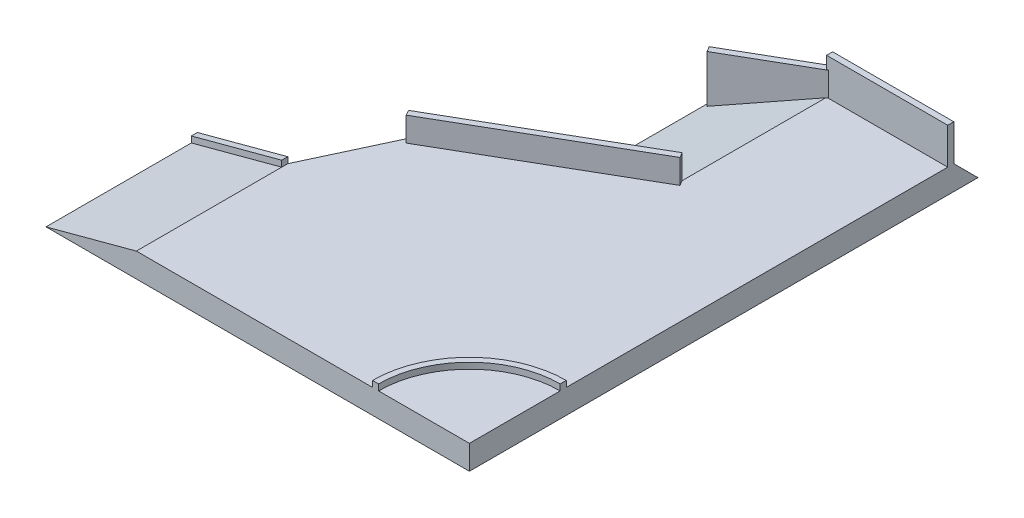
SolidWorks part; units mm, degrees
ref_plane "前视基准面" through (0, 0, 0) normal (0, 0, 1) x (1, 0, 0)
ref_plane "上视基准面" through (0, 0, 0) normal (0, 1, 0) x (1, 0, 0)
ref_plane "右视基准面" through (0, 0, 0) normal (1, 0, 0) x (0, 0, -1)
sketch "草图1" plane through (0, 0, 0) normal (0, 1, 0) x (1, 0, 0)
  line L0 (-2750, -1500) -> (-2116.0726, -140.5383)
  line L1 (-2750, -4000) -> (2750, -4000)
  line L2 (-2750, -4000) -> (-2750, -1500)
  line L3 (750, 4000) -> (2750, 4000)
  line L4 (2750, -4000) -> (2750, 4000)
  line L5 (-2750, -4000) -> (2750, 4000) construction
  line L6 (-532.1025, 773.9673) -> (2750, -4000) construction
  line L7 (-2116.0726, -140.5383) -> (750, 1514.1895)
  line L8 (750, 1514.1895) -> (750, 4000)
  point P0 (0, 0)
  dimension "D1" = 8000
  dimension "D2" = 5500
  dimension "D3" = 2500
  dimension "D4" = 2000
  dimension "D5" = 1500
  dimension "D6" = 120
  dimension "D7" = 145
  dimension "D8" = 90
extrude "凸台-拉伸1" add sketch "草图1" along normal blind 400
sketch "草图2" plane through (0, 400, 0) normal (0, 1, 0) x (1, 0, 0)
  line L0 (1150, -4000) -> (1250, -4000)
  line L1 (2750, -2500) -> (2750, -2400)
  arc A0 (2750, -2500) -> (1250, -4000) centre (2750, -4000) ccw
  arc A1 (2750, -2400) -> (1150, -4000) centre (2750, -4000) ccw
  dimension "D1" = 3200
  dimension "D2" = 3000
extrude "凸台-拉伸2" add sketch "草图2" along normal blind 100
sketch "草图3" plane through (0, 400, 0) normal (0, 1, 0) x (1, 0, 0)
  line L0 (750, 4000) -> (750, 1514.1895) construction
  line L1 (2750, 4000) -> (750, 4000)
  line L2 (2750, 4000) -> (2750, 3900)
  line L3 (2750, 3900) -> (750, 3900)
  line L4 (750, 4000) -> (750, 3900)
  dimension "D1" = 100
extrude "凸台-拉伸3" add sketch "草图3" along normal blind 600
sketch "草图4" plane through (0, 400, 0) normal (0, 1, 0) x (1, 0, 0)
  line L0 (750, 1514.1895) -> (-2116.0726, -140.5383)
  line L1 (750, 1514.1895) -> (800, 1427.5869)
  line L2 (-2116.0726, -140.5383) -> (-2066.0726, -227.1409)
  line L3 (800, 1427.5869) -> (-2066.0726, -227.1409)
  dimension "D1" = 100
extrude "凸台-拉伸4" add sketch "草图4" along normal blind 400
sketch "草图5" plane through (0, 0, 4000) normal (0, 0, 1) x (1, 0, 0)
  line L0 (-2750, 400) -> (-2750, 0)
  line L1 (-2750, 0) -> (-4242.8203, 0)
  line L2 (-4242.8203, 0) -> (-2750, 400)
  dimension "D1" = 15
extrude "凸台-拉伸5" add sketch "草图5" against normal blind 2500
sketch "草图6" plane through (0, 0, 1500) normal (0, 0, -1) x (-1, 0, 0)
  line L0 (2750, 400) -> (4242.8203, 0)
  line L1 (4242.8203, 0) -> (4242.8203, 100)
  line L2 (4242.8203, 100) -> (2750, 500)
  line L3 (2750, 500) -> (2750, 400)
  dimension "D1" = 100
extrude "凸台-拉伸6" add sketch "草图6" against normal blind 100
sketch "草图7" plane through (-1647.9093, 0, 951.4209) normal (-0.866, 0, 0.5) x (0.5, 0, 0.866)
  line L0 (-936.3265, 0) -> (-1336.3265, 0)
  line L1 (-1336.3265, 0) -> (-936.3265, 400)
  line L2 (-936.3265, 400) -> (-936.3265, 0)
  dimension "D1" = 45
extrude "凸台-拉伸7" add sketch "草图7" against normal up to next
ref_plane "基准面1" through (-1544.5508, 0, -2675.2405) normal (0.5, 0, 0.866) x (0, -1, 0)
sketch "草图8" plane through (-1544.5508, 0, -2675.2405) normal (0.5, 0, 0.866) x (0, -1, 0)
  line L0 (0, 2649.5191) -> (-400, 2649.5191)
  line L1 (-1000, 2649.5191) -> (0, 2649.5191) construction
  line L2 (-400, 2649.5191) -> (0, 1156.6987)
  line L3 (0, 1156.6987) -> (0, 2649.5191)
  dimension "D1" = 400
  dimension "D2" = 15
extrude "凸台-拉伸8" add sketch "草图8" along direction (0, 0, 1) on the side of the normal up to surface (2485.8105 mm away)
sketch "草图9" plane through (2750, 0, 0) normal (1, 0, 0) x (0, 0, -1)
  line L0 (4000, 0) -> (4400, 0)
  line L1 (4400, 0) -> (4000, 400)
  line L2 (4000, 1000) -> (4000, 0) construction
  line L3 (4000, 400) -> (4000, 0)
  dimension "D1" = 400
  dimension "D2" = 45
ref_plane "基准面3" through (2294.5508, 0, -1324.7595) normal (-0.866, 0, 0.5) x (0, 1, 0)
ref_plane "基准面4" through (1699.7595, 0, -455.4492) normal (-0.9659, 0, 0.2588) x (0, 1, 0)
extrude "凸台-拉伸10" add sketch "草图9" against normal up to surface (2107.1797 mm away) up to plane "基准面4"
sketch "草图11" plane through (2294.5508, 0, -1324.7595) normal (-0.866, 0, 0.5) x (0, 1, 0)
  line L0 (400, 3089.1016) -> (0, 3089.1016)
  line L1 (0, 3089.1016) -> (0, 3489.1016)
  line L2 (0, 3489.1016) -> (400, 3089.1016)
  dimension "D1" = 45
extrude "凸台-拉伸11" add sketch "草图11" along normal up to vertex (1492.8203 mm away) and the other way up to surface other way up to face at (714.2734, 133.3333, -4133.3333)
sketch "草图12" plane through (-1544.5508, 0, -2675.2405) normal (0.5, 0, 0.866) x (0.866, 0, -0.5)
  line L0 (2649.5191, 1000) -> (2649.5191, 400) construction
  line L1 (1156.6987, 0) -> (2649.5191, 0)
  line L2 (1156.6987, 0) -> (1156.6987, 800)
  line L3 (1156.6987, 800) -> (2649.5191, 800)
  line L4 (2649.5191, 0) -> (2649.5191, 800)
  dimension "D1" = 800
  dimension "D2" = 0
extrude "凸台-拉伸12" add sketch "草图12" along normal blind 100
